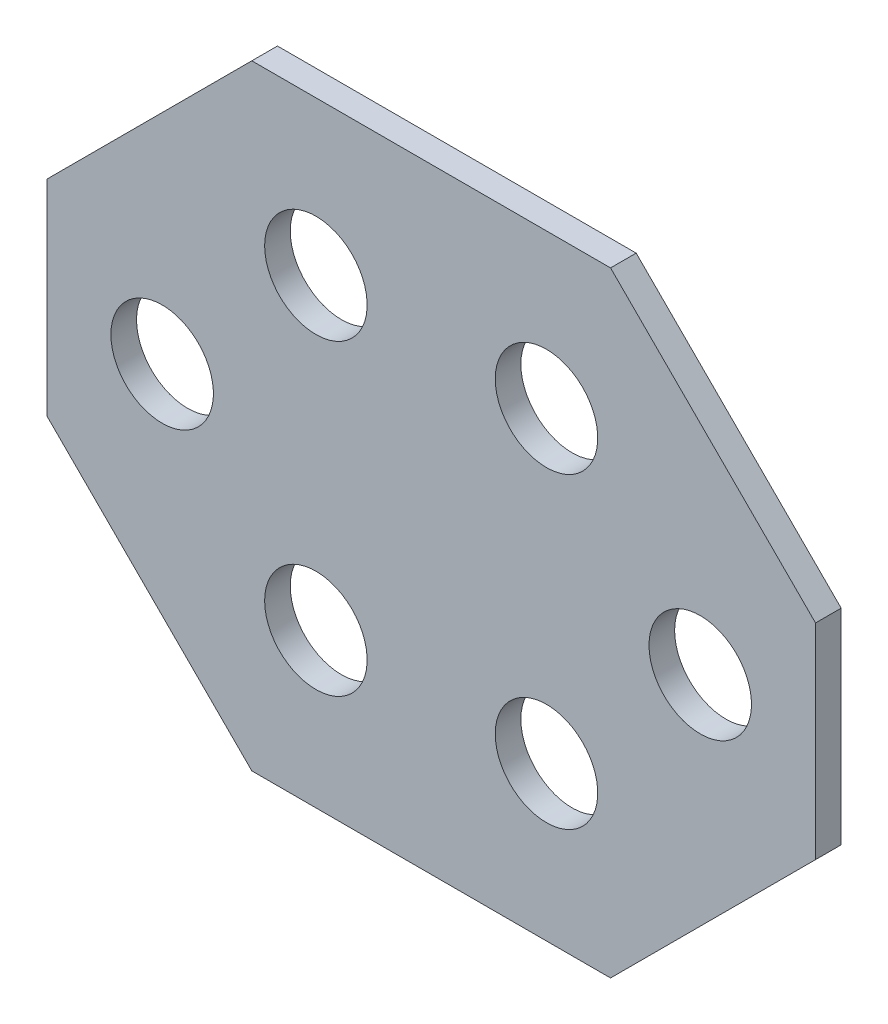
SolidWorks part; units mm, degrees
material "1060 Alloy"
ref_plane "Front Plane" through (0, 0, 0) normal (0, 0, 1) x (1, 0, 0)
ref_plane "Top Plane" through (0, 0, 0) normal (0, 1, 0) x (1, 0, 0)
ref_plane "Right Plane" through (0, 0, 0) normal (1, 0, 0) x (0, 0, -1)
sketch "Sketch1" plane through (0, 0, 0) normal (0, 0, 1) x (1, 0, 0)
  line L1 (15, -12) -> (-15, -12)
  line L2 (15, -12) -> (15, 12)
  line L3 (15, 12) -> (-15, 12)
  line L4 (-15, -12) -> (-15, 12)
  line L5 (15, -12) -> (-15, 12) construction
  line L6 (15, 12) -> (-15, -12) construction
  dimension "D1" = 24
  dimension "D2" = 30
extrude "Boss-Extrude1" add sketch "Sketch1" along normal blind 1 contours L4 L3 L2 L1
sketch "Sketch3" plane through (0, 0, 0) normal (0, 0, -1) x (-1, 0, 0)
  line L0 (0, 0) -> (-10.5, 0) construction
  line L1 (-4.5, 0) -> (-4.5, 6) construction
  line L2 (-4.5, 0) -> (-4.5, -6) construction
  circle A0 centre (-4.5, 6) radius 2
  circle A1 centre (-4.5, -6) radius 2
  circle A2 centre (-10.5, 0) radius 2
  dimension "D5" = 4
  dimension "D1" = 4.5
  dimension "D2" = 10.5
  dimension "D3" = 6
  dimension "D4" = 6
extrude "Cut-Extrude1" cut sketch "Sketch3" against normal blind 3
chamfer "Chamfer1" distance 8 angle 45 4 edges at (15, -12, 0.5) (15, 12, 0.5) (-15, 12, 0.5) (-15, -12, 0.5)
ref_plane "Plane1" through (0, 0, 0) normal (1, 0, 0) x (0, 0, -1)
mirror "Mirror1" about plane through (0, 0, 0) normal (1, 0, 0) of "Cut-Extrude1"
